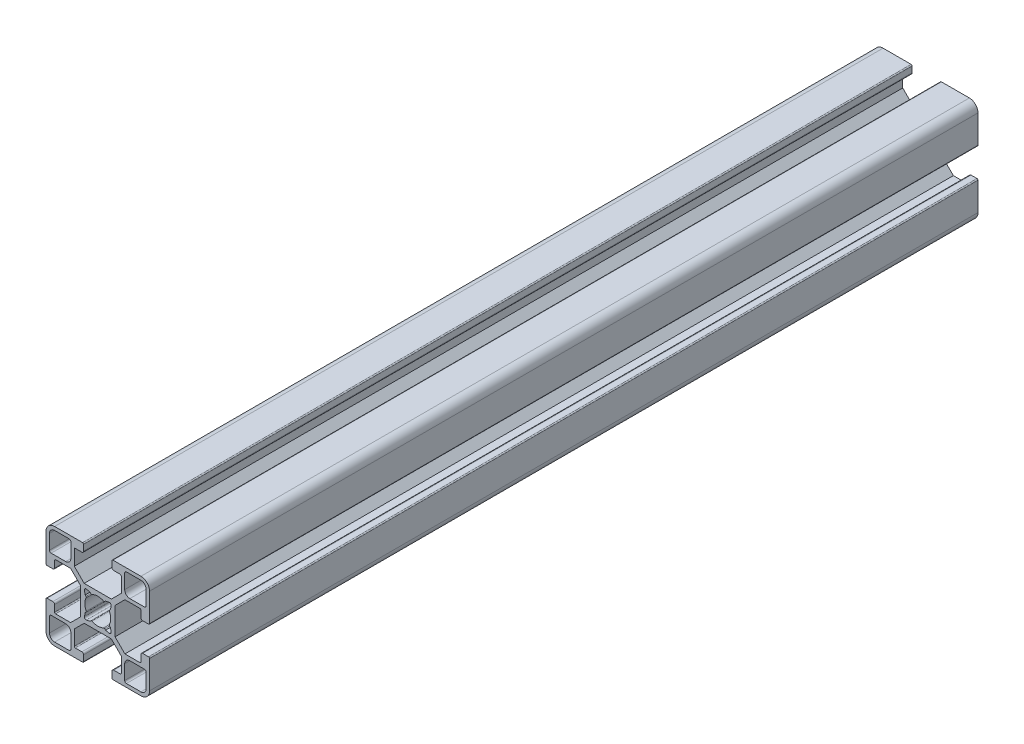
SolidWorks part; units mm, degrees
ref_plane "Front Plane" through (0, 0, 0) normal (0, 0, 1) x (1, 0, 0)
ref_plane "Top Plane" through (0, 0, 0) normal (0, 1, 0) x (1, 0, 0)
ref_plane "Right Plane" through (0, 0, 0) normal (1, 0, 0) x (0, 0, -1)
sketch "Sketch1" plane through (0, 0, 0) normal (0, 0, 1) x (1, 0, 0)
  line L0 (18.8789, 11.7141) -> (18.6573, 12.7569)
  line L1 (11.3427, 17.2431) -> (11.1211, 18.2859)
  line L2 (12.9949, 18.4193) -> (12.7569, 18.6573)
  line L3 (21.8, 7.1394) -> (18.9393, 10)
  line L4 (22.8607, 8.2) -> (20, 11.0607)
  line L5 (11.5807, 17.0051) -> (11.3427, 17.2431)
  line L6 (17.2431, 11.3427) -> (17.0051, 11.5806)
  line L7 (10, 18.9393) -> (7.1393, 21.8)
  line L8 (11.0607, 20) -> (8.2, 22.8606)
  line L9 (18.6573, 12.7569) -> (18.4193, 12.9948)
  line L10 (18.2859, 11.1211) -> (17.2431, 11.3427)
  line L11 (12.7569, 18.6573) -> (11.7141, 18.8789)
  line L12 (2.5, 0) -> (10.6, 0)
  line L13 (19.4, 0) -> (27.5, 0)
  line L14 (23.3, 1) -> (27.5, 1)
  line L15 (2.5, 1) -> (6.7, 1)
  line L16 (8.5, 2.5) -> (10.4, 2.5)
  line L17 (19.6, 2.5) -> (21.5, 2.5)
  line L18 (24.3, 7.2) -> (28.5, 7.2)
  line L19 (1.5, 7.2) -> (5.7, 7.2)
  line L20 (2.8, 8.2) -> (7.1393, 8.2)
  line L21 (22.8607, 8.2) -> (27.2, 8.2)
  line L22 (11.0607, 10) -> (18.9393, 10)
  line L23 (0.3, 10.9) -> (2, 10.9)
  line L24 (28, 10.9) -> (29.7, 10.9)
  line L25 (0.3, 19.1) -> (2, 19.1)
  line L26 (28, 19.1) -> (29.7, 19.1)
  line L27 (11.0607, 20) -> (18.9393, 20)
  line L28 (2.8, 21.8) -> (7.1393, 21.8)
  line L29 (22.8607, 21.8) -> (27.2, 21.8)
  line L30 (1.5, 22.8) -> (5.7, 22.8)
  line L31 (24.3, 22.8) -> (28.5, 22.8)
  line L32 (19.6, 27.5) -> (21.5, 27.5)
  line L33 (8.5, 27.5) -> (10.4, 27.5)
  line L34 (2.5, 29) -> (6.7, 29)
  line L35 (23.3, 29) -> (27.5, 29)
  line L36 (19.4, 30) -> (27.5, 30)
  line L37 (2.5, 30) -> (10.6, 30)
  line L38 (11.7141, 11.1211) -> (12.7569, 11.3427)
  line L39 (17.2431, 18.6573) -> (18.2859, 18.8789)
  line L40 (18.4194, 17.0051) -> (18.6573, 17.2431)
  line L41 (8.2, 7.1393) -> (11.0607, 10)
  line L42 (7.1393, 8.2) -> (10, 11.0607)
  line L43 (12.7569, 11.3427) -> (12.9949, 11.5806)
  line L44 (11.3427, 12.7569) -> (11.5807, 12.9949)
  line L45 (20, 18.9393) -> (22.8607, 21.8)
  line L46 (18.9393, 20) -> (21.8, 22.8606)
  line L47 (17.0051, 18.4193) -> (17.2431, 18.6573)
  line L48 (11.1211, 11.7141) -> (11.3427, 12.7569)
  line L49 (18.6573, 17.2431) -> (18.8789, 18.2859)
  line L50 (0, 19.4) -> (0, 27.5)
  line L51 (0, 2.5) -> (0, 10.6)
  line L52 (1, 23.3) -> (1, 27.5)
  line L53 (1, 2.5) -> (1, 6.7)
  line L54 (2.5, 8.5) -> (2.5, 10.4)
  line L55 (2.5, 19.6) -> (2.5, 21.5)
  line L56 (7.2, 24.3) -> (7.2, 28.5)
  line L57 (7.2, 1.5) -> (7.2, 5.7)
  line L58 (8.2, 2.8) -> (8.2, 7.1393)
  line L59 (8.2, 22.8606) -> (8.2, 27.2)
  line L60 (10, 11.0607) -> (10, 18.9393)
  line L61 (10.9, 0.3) -> (10.9, 2)
  line L62 (10.9, 28) -> (10.9, 29.7)
  line L63 (19.1, 0.3) -> (19.1, 2)
  line L64 (19.1, 28) -> (19.1, 29.7)
  line L65 (20, 11.0607) -> (20, 18.9393)
  line L66 (21.8, 2.8) -> (21.8, 7.1394)
  line L67 (21.8, 22.8606) -> (21.8, 27.2)
  line L68 (22.8, 24.3) -> (22.8, 28.5)
  line L69 (22.8, 1.5) -> (22.8, 5.7)
  line L70 (27.5, 8.5) -> (27.5, 10.4)
  line L71 (27.5, 19.6) -> (27.5, 21.5)
  line L72 (29, 23.3) -> (29, 27.5)
  line L73 (29, 2.5) -> (29, 6.7)
  line L74 (30, 2.5) -> (30, 10.6)
  line L75 (30, 19.4) -> (30, 27.5)
  line L76 (15, 36.6844) -> (15, -6.6844) construction
  line L77 (-9.3806, 15) -> (40.1263, 15) construction
  arc A0 (0.3, 10.9) -> (0, 10.6) centre (0.3, 10.6) ccw
  arc A1 (0, 19.4) -> (0.3, 19.1) centre (0.3, 19.4) ccw
  arc A2 (1.5, 7.2) -> (1, 6.7) centre (1.5, 6.7) ccw
  arc A3 (1, 23.3) -> (1.5, 22.8) centre (1.5, 23.3) ccw
  arc A4 (2.5, 10.4) -> (2, 10.9) centre (2, 10.4) ccw
  arc A5 (2, 19.1) -> (2.5, 19.6) centre (2, 19.6) ccw
  arc A6 (1, 2.5) -> (2.5, 1) centre (2.5, 2.5) ccw
  arc A7 (0, 2.5) -> (2.5, 0) centre (2.5, 2.5) ccw
  arc A8 (2.5, 29) -> (1, 27.5) centre (2.5, 27.5) ccw
  arc A9 (2.5, 30) -> (0, 27.5) centre (2.5, 27.5) ccw
  arc A10 (2.5, 8.5) -> (2.8, 8.2) centre (2.8, 8.5) ccw
  arc A11 (2.8, 21.8) -> (2.5, 21.5) centre (2.8, 21.5) ccw
  arc A12 (7.2, 5.7) -> (5.7, 7.2) centre (5.7, 5.7) ccw
  arc A13 (5.7, 22.8) -> (7.2, 24.3) centre (5.7, 24.3) ccw
  arc A14 (6.7, 1) -> (7.2, 1.5) centre (6.7, 1.5) ccw
  arc A15 (7.2, 28.5) -> (6.7, 29) centre (6.7, 28.5) ccw
  arc A16 (8.2, 2.8) -> (8.5, 2.5) centre (8.5, 2.8) ccw
  arc A17 (8.5, 27.5) -> (8.2, 27.2) centre (8.5, 27.2) ccw
  arc A18 (10.9, 2) -> (10.4, 2.5) centre (10.4, 2) ccw
  arc A19 (10.4, 27.5) -> (10.9, 28) centre (10.4, 28) ccw
  arc A20 (10.6, 0) -> (10.9, 0.3) centre (10.6, 0.3) ccw
  arc A21 (10.9, 29.7) -> (10.6, 30) centre (10.6, 29.7) ccw
  arc A22 (11.5807, 12.9949) -> (11.6375, 13.3398) centre (11.3685, 13.207) ccw
  arc A23 (11.6375, 16.6602) -> (11.5807, 17.0051) centre (11.3685, 16.793) ccw
  arc A24 (11.1211, 11.7141) -> (11.7141, 11.1211) centre (11.6102, 11.6102) ccw
  arc A25 (11.7141, 18.8789) -> (11.1211, 18.2859) centre (11.6102, 18.3898) ccw
  arc A26 (13.3398, 11.6375) -> (12.9949, 11.5806) centre (13.207, 11.3685) ccw
  arc A27 (12.9949, 18.4193) -> (13.3398, 18.3625) centre (13.207, 18.6315) ccw
  arc A28 (11.6375, 16.6602) -> (11.6375, 13.3398) centre (15, 15) ccw
  arc A29 (16.6602, 18.3625) -> (13.3398, 18.3625) centre (15, 15) ccw
  arc A30 (18.3625, 13.3398) -> (18.3625, 16.6602) centre (15, 15) ccw
  arc A31 (13.3398, 11.6375) -> (16.6602, 11.6375) centre (15, 15) ccw
  arc A32 (17.0051, 11.5806) -> (16.6602, 11.6375) centre (16.793, 11.3685) ccw
  arc A33 (16.6602, 18.3625) -> (17.0051, 18.4193) centre (16.793, 18.6315) ccw
  arc A34 (18.2859, 11.1211) -> (18.8789, 11.7141) centre (18.3898, 11.6102) ccw
  arc A35 (18.8789, 18.2859) -> (18.2859, 18.8789) centre (18.3898, 18.3898) ccw
  arc A36 (18.3625, 13.3398) -> (18.4193, 12.9948) centre (18.6315, 13.207) ccw
  arc A37 (18.4194, 17.0051) -> (18.3625, 16.6602) centre (18.6315, 16.793) ccw
  arc A38 (19.1, 0.3) -> (19.4, 0) centre (19.4, 0.3) ccw
  arc A39 (19.4, 30) -> (19.1, 29.7) centre (19.4, 29.7) ccw
  arc A40 (19.6, 2.5) -> (19.1, 2) centre (19.6, 2) ccw
  arc A41 (19.1, 28) -> (19.6, 27.5) centre (19.6, 28) ccw
  arc A42 (21.5, 2.5) -> (21.8, 2.8) centre (21.5, 2.8) ccw
  arc A43 (21.8, 27.2) -> (21.5, 27.5) centre (21.5, 27.2) ccw
  arc A44 (22.8, 1.5) -> (23.3, 1) centre (23.3, 1.5) ccw
  arc A45 (23.3, 29) -> (22.8, 28.5) centre (23.3, 28.5) ccw
  arc A46 (24.3, 7.2) -> (22.8, 5.7) centre (24.3, 5.7) ccw
  arc A47 (22.8, 24.3) -> (24.3, 22.8) centre (24.3, 24.3) ccw
  arc A48 (27.2, 8.2) -> (27.5, 8.5) centre (27.2, 8.5) ccw
  arc A49 (27.5, 21.5) -> (27.2, 21.8) centre (27.2, 21.5) ccw
  arc A50 (27.5, 1) -> (29, 2.5) centre (27.5, 2.5) ccw
  arc A51 (27.5, 0) -> (30, 2.5) centre (27.5, 2.5) ccw
  arc A52 (29, 27.5) -> (27.5, 29) centre (27.5, 27.5) ccw
  arc A53 (30, 27.5) -> (27.5, 30) centre (27.5, 27.5) ccw
  arc A54 (28, 10.9) -> (27.5, 10.4) centre (28, 10.4) ccw
  arc A55 (27.5, 19.6) -> (28, 19.1) centre (28, 19.6) ccw
  arc A56 (29, 6.7) -> (28.5, 7.2) centre (28.5, 6.7) ccw
  arc A57 (28.5, 22.8) -> (29, 23.3) centre (28.5, 23.3) ccw
  arc A58 (30, 10.6) -> (29.7, 10.9) centre (29.7, 10.6) ccw
  arc A59 (29.7, 19.1) -> (30, 19.4) centre (29.7, 19.4) ccw
extrude "Boss-Extrude1" add sketch "Sketch1" along normal mid plane 240
equation "\"LENGTH\"=500"
